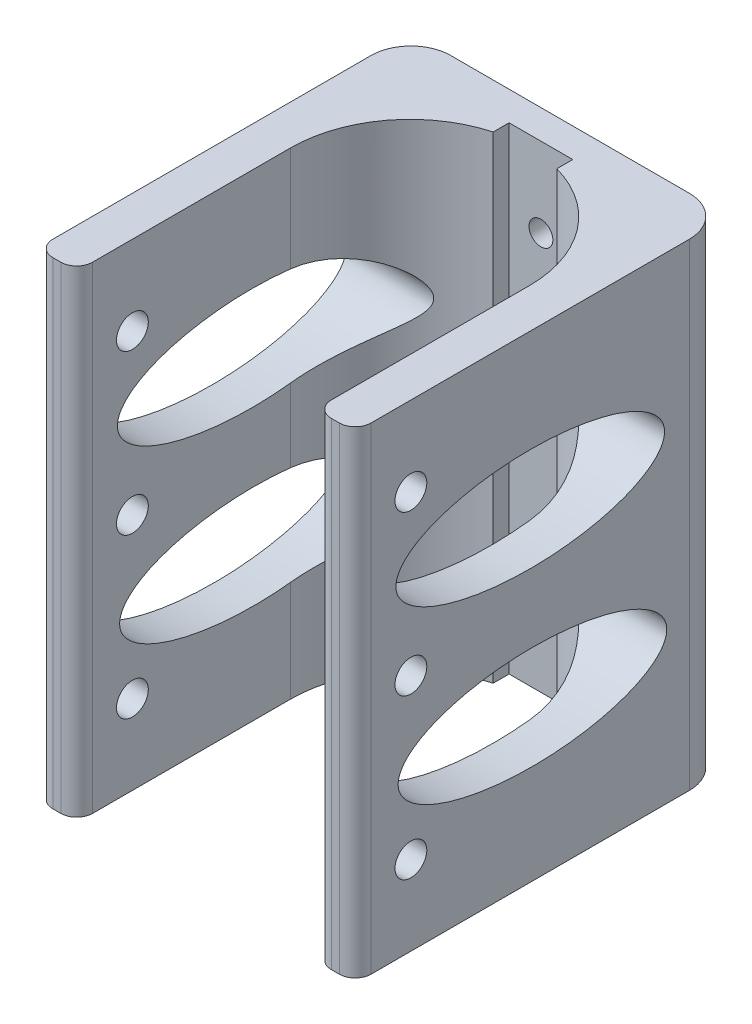
SolidWorks part; units mm, degrees
ref_plane "前视基准面" through (0, 0, 0) normal (0, 0, 1) x (1, 0, 0)
ref_plane "上视基准面" through (0, 0, 0) normal (0, 1, 0) x (1, 0, 0)
ref_plane "右视基准面" through (0, 0, 0) normal (1, 0, 0) x (0, 0, -1)
sketch "草图1" plane through (0, 0, 0) normal (0, 1, 0) x (1, 0, 0)
  line L0 (-33.2887, -30.9797) -> (-33.2887, -6.0931)
  line L2 (-3.2887, -6.0931) -> (-3.2887, -30.9797)
  line L3 (-1.2887, -32.9797) -> (-0.2887, -32.9797)
  line L7 (-36.2887, -32.9797) -> (-35.2887, -32.9797)
  line L8 (-18.2887, 8.9069) -> (-18.2887, -6.0931) construction
  line L9 (1.7113, 9.0203) -> (1.7113, -30.9797)
  line L10 (-3.2887, -6.0931) -> (-33.2887, -6.0931) construction
  line L11 (-18.2887, 12.0203) -> (-14.2887, 12.0203) construction
  line L12 (-14.2887, 12.0203) -> (-22.2887, 12.0203) construction
  line L13 (-22.2887, 12.0203) -> (-22.2887, 8.9069) construction
  line L14 (-22.2887, 8.9069) -> (-14.2887, 8.9069) construction
  line L15 (-14.2887, 8.9069) -> (-14.2887, 12.0203) construction
  line L16 (-38.2887, 9.0203) -> (-38.2887, -30.9797)
  line L19 (-14.2887, 10.3637) -> (-22.2887, 10.3637)
  line L21 (-14.2887, 10.3637) -> (-14.2887, 8.3637)
  line L23 (-33.2887, 14.0203) -> (-3.2887, 14.0203)
  line L25 (-22.2887, 10.3637) -> (-22.2887, 8.3637)
  arc A0 (-33.2887, -6.0931) -> (-22.2887, 8.3637) centre (-18.2887, -6.0931) cw
  arc A1 (-14.2887, 8.3637) -> (-3.2887, -6.0931) centre (-18.2887, -6.0931) cw
  arc A2 (1.7113, 9.0203) -> (-3.2887, 14.0203) centre (-3.2887, 9.0203) ccw
  arc A3 (-33.2887, 14.0203) -> (-38.2887, 9.0203) centre (-33.2887, 9.0203) ccw
  arc A4 (-38.2887, -30.9797) -> (-36.2887, -32.9797) centre (-36.2887, -30.9797) ccw
  arc A5 (-33.2887, -30.9797) -> (-35.2887, -32.9797) centre (-35.2887, -30.9797) cw
  arc A6 (-3.2887, -30.9797) -> (-1.2887, -32.9797) centre (-1.2887, -30.9797) ccw
  arc A7 (-0.2887, -32.9797) -> (1.7113, -30.9797) centre (-0.2887, -30.9797) ccw
  point P30 (-3.2887, -32.9797)
  point P33 (1.7113, -32.9797)
  point P34 (-18.2887, 10.3637)
  dimension "D8" = 5
  dimension "D9" = 5
  dimension "D2" = 2
  dimension "D4" = 2
  dimension "D7" = 2
  dimension "D10" = 2
  dimension "D1" = 5
  dimension "D3" = 4
  dimension "D5" = 4
  dimension "D6" = 2
  dimension "D11" = 24.8865
  dimension "D12" = 3.6566
  dimension "D13" = 24.8865
extrude "凸台-拉伸1" add sketch "草图1" along normal blind 60
sketch "草图2" plane through (0, 0, -10.3637) normal (0, 0, 1) x (1, 0, 0)
  line L0 (-18.2887, 60) -> (-18.2887, 0) construction
  line L1 (-14.2887, 60) -> (-22.2887, 60) construction
  line L2 (-14.2887, 0) -> (-22.2887, 0) construction
  line L3 (-18.2887, 0) -> (-18.2887, 30) construction
  line L4 (-18.2887, 30) -> (-18.2887, 50) construction
  line L5 (-18.2887, 50) -> (-18.2887, 30) construction
  line L6 (-18.2887, 30) -> (-18.2887, 10) construction
  circle A0 centre (-18.2887, 50) radius 1.5
  circle A1 centre (-18.2887, 30) radius 1.5
  circle A2 centre (-18.2887, 10) radius 1.5
extrude "切除-拉伸1" cut sketch "草图2" against normal blind 10
sketch "草图3" plane through (-38.2887, 0, 0) normal (-1, 0, 0) x (0, 0, 1)
  line L1 (-9.0203, 60) -> (30.9797, 60) construction
  line L2 (25.9797, 60) -> (25.9797, 0)
  line L3 (-9.0203, 0) -> (30.9797, 0) construction
  line L4 (25.9797, 0) -> (25.9797, 30)
  line L5 (25.9797, 30) -> (25.9797, 50)
  line L6 (25.9797, 50) -> (25.9797, 30)
  line L7 (25.9797, 30) -> (25.9797, 10)
  line L8 (-9.0203, 60) -> (-9.0203, 0) construction
  circle A0 centre (25.9797, 50) radius 2
  circle A1 centre (25.9797, 30) radius 2
  circle A2 centre (25.9797, 10) radius 2
  dimension "D1" = 20
  dimension "D2" = 35
extrude "切除-拉伸2" cut sketch "草图3" against normal through all contours A2 | A1 | A0
sketch "草图4" plane through (1.7113, 0, 0) normal (1, 0, 0) x (0, 0, -1)
  line L0 (-10.9797, 60) -> (-10.9797, 0) construction
  line L1 (9.0203, 60) -> (-30.9797, 60) construction
  line L2 (9.0203, 0) -> (-30.9797, 0) construction
  line L3 (-10.9797, 0) -> (-30.9797, 30) construction
  line L4 (-30.9797, 60) -> (-30.9797, 0) construction
  line L5 (-30.9797, 30) -> (9.0203, 30) construction
  line L6 (9.0203, 60) -> (9.0203, 0) construction
  line L7 (9.0203, 30) -> (-10.9797, 15) construction
  line L8 (-10.9797, 15) -> (9.0203, 0) construction
  line L9 (9.0203, 0) -> (9.0203, 60) construction
  line L10 (9.0203, 60) -> (-10.9797, 30) construction
  line L11 (-10.9797, 30) -> (-10.9797, 60) construction
  line L12 (-10.9797, 60) -> (9.0203, 30) construction
  line L13 (9.0203, 30) -> (-10.9797, 45) construction
  line L14 (-10.9797, 45) -> (-30.9797, 60) construction
  ellipse E0 centre (-10.9797, 40.6206) end of major axis (5.8997, 40.6206) minor radius 6.4842
  ellipse E1 centre (-10.6997, 18.9524) end of major axis (6.1796, 18.9524) minor radius 6.4842
  point P21 (5.8997, 40.6206)
  point P27 (0, 0)
  point P28 (8.2341, 15)
  point P34 (-12.648, 26.7443)
  point P35 (-10.9797, 22.0757)
  point P36 (0, 0)
  point P37 (0, 0)
extrude "切除-拉伸3" cut sketch "草图4" against normal through all both and the other way through all
